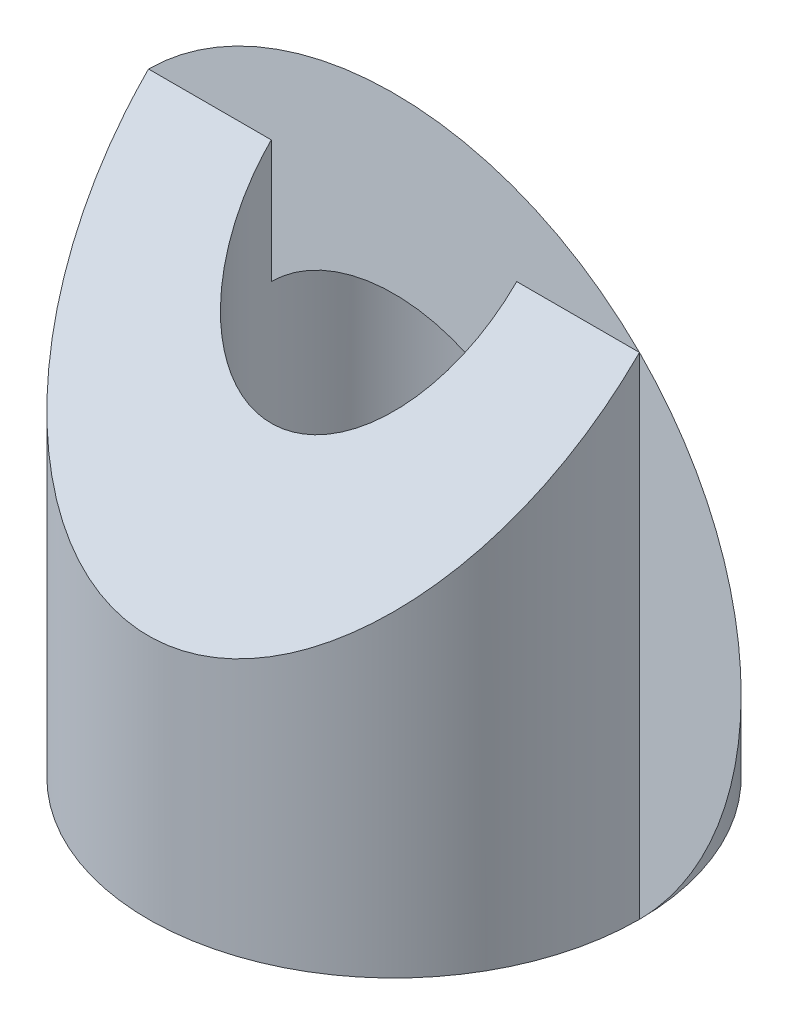
SolidWorks part; units mm, degrees
ref_plane "Front" through (0, 0, 0) normal (0, 0, 1) x (1, 0, 0)
ref_plane "Top" through (0, 0, 0) normal (0, 1, 0) x (1, 0, 0)
ref_plane "Right" through (0, 0, 0) normal (1, 0, 0) x (0, 0, -1)
sketch "Sketch1" plane through (0, 0, 0) normal (0, 1, 0) x (1, 0, 0)
  circle A0 centre (0, 0) radius 2
  circle A1 centre (0, 0) radius 1
  dimension "D1" = 4
  dimension "D2" = 2
extrude "Boss-Extrude1" add sketch "Sketch1" along normal blind 4
sketch "Sketch2" plane through (0, 0, 0) normal (1, 0, 0) x (0, 0, -1)
  line L0 (-2, 2) -> (0, 4)
  line L1 (-2, 4) -> (-2, 0) construction
  line L2 (2, 4) -> (-2, 4) construction
  line L6 (0, 4) -> (-2, 4)
  line L7 (-2, 4) -> (-2, 2)
extrude "Cut-Extrude1" cut sketch "Sketch2" against normal mid plane 4
sketch "Sketch3" plane through (0, 0, 0) normal (0, 0, 1) x (1, 0, 0)
  line L0 (2, 0) -> (-2, 4)
  line L1 (-2, 4) -> (2, 4)
  line L2 (2, 4) -> (2, 0)
  point P6 (0, 0)
  point P7 (0, 0)
extrude "Cut-Extrude2" cut sketch "Sketch3" against normal blind 10
